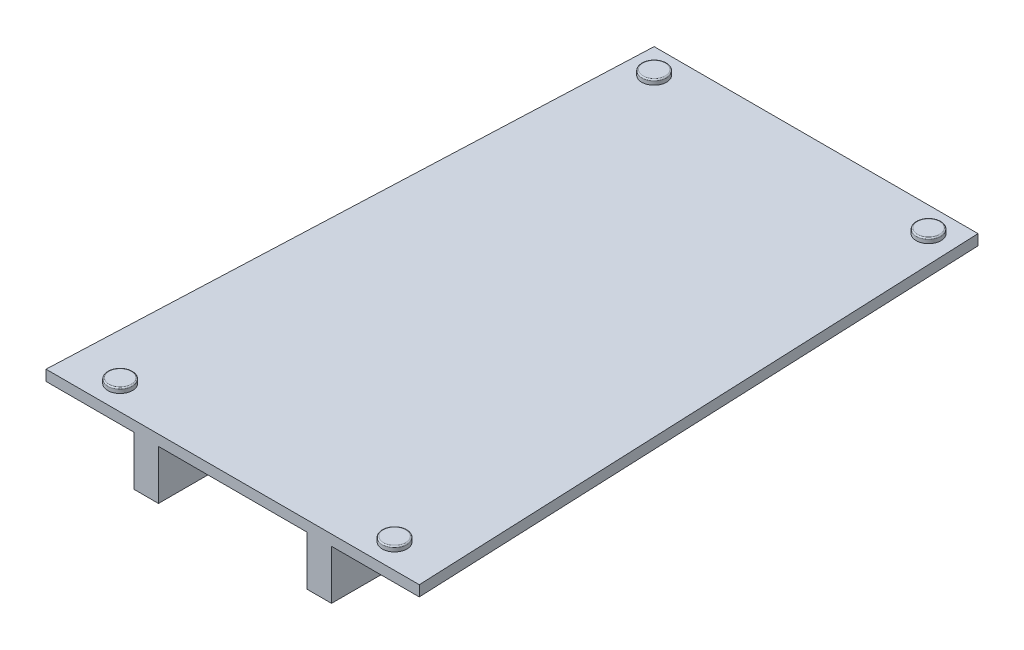
SolidWorks part; units mm, degrees
ref_plane "Front Plane" through (0, 0, 0) normal (0, 0, 1) x (1, 0, 0)
ref_plane "Top Plane" through (0, 0, 0) normal (0, 1, 0) x (1, 0, 0)
ref_plane "Right Plane" through (0, 0, 0) normal (1, 0, 0) x (0, 0, -1)
sketch "Sketch2" plane through (0, 0, 0) normal (0, 1, 0) x (1, 0, 0)
  line L0 (0, -118) -> (0, 118)
  line L1 (-65.5, 118) -> (65.5, 118)
  line L2 (-75.5, -118) -> (75.5, -118)
  line L3 (-65.5, 118) -> (-75.5, -118)
  line L4 (65.5, 118) -> (75.5, -118)
  point P4 (0, 0)
  point P7 (0, 118)
  point P10 (0, -118)
  dimension "D1" = 151
  dimension "D2" = 131
  dimension "D3" = 236
extrude "Boss-Extrude1" add sketch "Sketch2" along normal blind 4.3 contours L1 L3 L2 L0 | L4 L1 L0 L2
sketch "Sketch3" plane through (0, 0, 0) normal (0, -1, 0) x (1, 0, 0)
  line L0 (-30, 0) -> (30, 0) construction
  line L1 (-30, -118) -> (-30, 118)
  line L2 (-75.5, 118) -> (75.5, 118) construction
  line L3 (30, -118) -> (30, 118)
  line L4 (-30, 118) -> (-40, 118)
  line L5 (-40, 118) -> (-40, -118)
  line L6 (-65.5, -118) -> (65.5, -118) construction
  line L7 (-40, -118) -> (-30, -118)
  line L8 (30, 118) -> (40, 118)
  line L9 (40, 118) -> (40, -118)
  line L10 (40, -118) -> (30, -118)
  point P4 (0, 0)
  point P10 (-30, 0)
  point P13 (30, 0)
  dimension "D1" = 60
  dimension "D2" = 10
extrude "Boss-Extrude2" add sketch "Sketch3" along normal blind 20
sketch "Sketch4" plane through (0, 4.3, 0) normal (0, 1, 0) x (1, 0, 0)
  line L0 (-55.5, 118) -> (-55.5, 108) construction
  line L1 (-65.5, 118) -> (65.5, 118) construction
  line L2 (0, 0) -> (0, 33.6432) construction
  line L3 (0, 0) -> (27.053, 0) construction
  circle A0 centre (-55.5, 108) radius 5
  circle A1 centre (55.5, 108) radius 5
  circle A2 centre (-55.5, -108) radius 5
  circle A3 centre (55.5, -108) radius 5
  dimension "D3" = 10
  dimension "D1" = 10
  dimension "D2" = 10
extrude "Boss-Extrude3" add sketch "Sketch4" along normal blind 2
fillet "Fillet1" radius 0.5 4 edges at (-55.5, 6.3, -103) (-55.5, 6.3, 103) (55.5, 6.3, 113) (55.5, 6.3, -113)
sketch "Sketch5" plane through (-40, 0, 0) normal (-1, 0, 0) x (0, 0, 1)
  line L0 (0, 0) -> (0, -20) construction
  line L1 (118, -20) -> (-118, -20) construction
  line L2 (-59, -10) -> (59, -10) construction
  circle A0 centre (-59, -10) radius 2.5
  circle A1 centre (59, -10) radius 2.5
  point P8 (0, -10)
  dimension "D2" = 5
  dimension "D1" = 118
extrude "Cut-Extrude1" cut sketch "Sketch5" against normal through all and the other way through all
